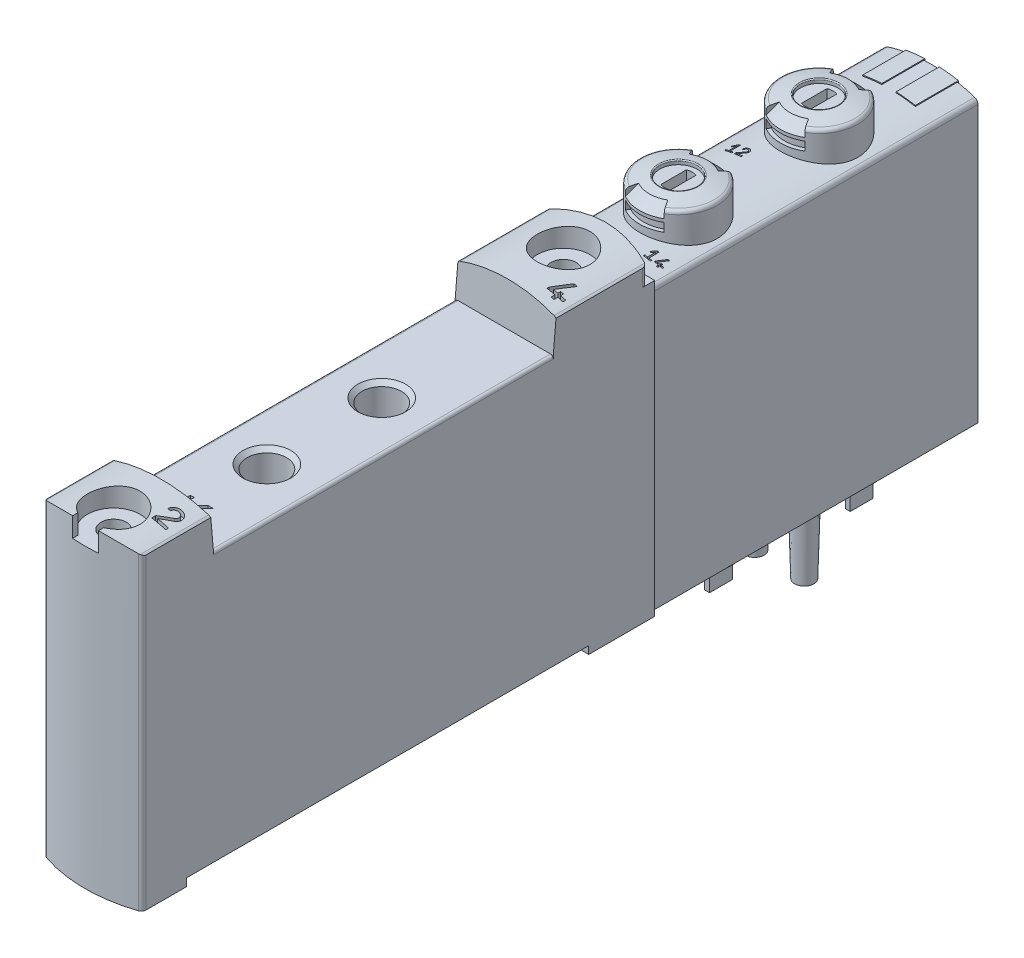
SolidWorks part; units mm, degrees
ref_plane "Front Plane" through (0, 0, 0) normal (0, 0, 1) x (1, 0, 0)
ref_plane "Top Plane" through (0, 0, 0) normal (0, 1, 0) x (1, 0, 0)
ref_plane "Right Plane" through (0, 0, 0) normal (1, 0, 0) x (0, 0, -1)
ref_plane "Plane1" through (0, 0, -23.2) normal (0, 0, 1) x (1, 0, 0)
sketch "Sketch1" plane through (0, 0, -23.2) normal (0, 0, 1) x (1, 0, 0)
  line L0 (-4.9, 29.2163) -> (-4.9, 0)
  line L1 (-4.9, 0) -> (4.9, 0)
  line L2 (4.9, 0) -> (4.9, 29.2163)
  arc A0 (4.9, 29.2163) -> (4.5517, 29.6927) centre (4.4, 29.2163) ccw
  arc A1 (4.5517, 29.6927) -> (-4.5517, 29.6927) centre (0, 15.4) ccw
  arc A2 (-4.5517, 29.6927) -> (-4.9, 29.2163) centre (-4.4, 29.2163) ccw
extrude "Boss-Extrude1" add sketch "Sketch1" along normal blind 34
ref_plane "Plane2" through (0, 0, 0) normal (1, 0, 0) x (0, 0, -1)
sketch "Sketch2" plane through (0, 0, 0) normal (1, 0, 0) x (0, 0, -1)
  line L0 (-10.88, 0.4) -> (-10.88, 0)
  line L1 (-10.88, 0) -> (23.22, 0)
  line L2 (23.22, 0) -> (23.22, 0.4)
  line L3 (23.22, 0.4) -> (-10.88, 0.4)
extrude "Cut-Extrude1" cut sketch "Sketch2" against normal blind 6 and the other way blind 6
ref_plane "Plane3" through (0, 0, 0) normal (0, 1, 0) x (1, 0, 0)
sketch "Sketch3" plane through (0, 0, 0) normal (0, 1, 0) x (1, 0, 0)
  line L0 (-3.15, 2.4653) -> (-3.15, -2.4653)
  line L1 (3.15, -2.4653) -> (3.15, 2.4653)
  arc A0 (-3.15, -2.4653) -> (3.15, -2.4653) centre (0, 0) ccw
  arc A1 (3.15, 2.4653) -> (-3.15, 2.4653) centre (0, 0) ccw
extrude "Cut-Extrude2" cut sketch "Sketch3" along normal blind 1.9
ref_plane "Plane4" through (0, 0, 0) normal (0, 1, 0) x (1, 0, 0)
sketch "Sketch4" plane through (0, 0, 0) normal (0, 1, 0) x (1, 0, 0)
  line L0 (-3.15, 17.1653) -> (-3.15, 12.2347)
  line L1 (3.15, 12.2347) -> (3.15, 17.1653)
  arc A0 (-3.15, 12.2347) -> (3.15, 12.2347) centre (0, 14.7) ccw
  arc A1 (3.15, 17.1653) -> (-3.15, 17.1653) centre (0, 14.7) ccw
extrude "Cut-Extrude3" cut sketch "Sketch4" along normal blind 1.9
ref_plane "Plane5" through (0, 0, 0) normal (1, 0, 0) x (0, 0, -1)
sketch "Sketch5" plane through (0, 0, 0) normal (1, 0, 0) x (0, 0, -1)
  line L0 (0, 2.1) -> (3.05, 2.1)
  line L1 (3.05, 2.1) -> (3.05, 1.1)
  line L2 (3.05, 1.1) -> (2.25, 1.1)
  line L3 (2.25, 1.1) -> (2.25, -1.4)
  line L4 (2.25, -1.4) -> (2.65, -1.4)
  line L5 (2.65, -1.4) -> (2.65, -1.72)
  line L6 (2.65, -1.72) -> (2.4306, -2.1)
  line L7 (2.4306, -2.1) -> (0, -2.1)
  line L8 (0, -2.1) -> (0, 2.1)
  line L9 (0, -2.1) -> (0, 2.1) construction
revolve "Revolve1" add sketch "Sketch5" angle 360 about L9
ref_plane "Plane6" through (0, 0, 0) normal (1, 0, 0) x (0, 0, -1)
sketch "Sketch6" plane through (0, 0, 0) normal (1, 0, 0) x (0, 0, -1)
  line L0 (14.7, 2.1) -> (17.75, 2.1)
  line L1 (17.75, 2.1) -> (17.75, 1.1)
  line L2 (17.75, 1.1) -> (16.95, 1.1)
  line L3 (16.95, 1.1) -> (16.95, -1.4)
  line L4 (16.95, -1.4) -> (17.35, -1.4)
  line L5 (17.35, -1.4) -> (17.35, -1.72)
  line L6 (17.35, -1.72) -> (17.1306, -2.1)
  line L7 (17.1306, -2.1) -> (14.7, -2.1)
  line L8 (14.7, -2.1) -> (14.7, 2.1)
  line L9 (14.7, -2.1) -> (14.7, 2.1) construction
revolve "Revolve2" add sketch "Sketch6" angle 360 about L9
ref_plane "Plane7" through (0, 0, -7.35) normal (0, 0, 1) x (1, 0, 0)
sketch "Sketch7" plane through (0, 0, -7.35) normal (0, 0, 1) x (1, 0, 0)
  line L0 (2.6, 0.4) -> (3.8, 0.4)
  line L1 (3.8, 0.4) -> (3.6, -6.9)
  line L2 (2.6, -7.0623) -> (2.6, 0.4)
  line L3 (2.6, -7.0623) -> (2.6, 0.4) construction
  arc A0 (3.6, -6.9) -> (2.6, -7.0623) centre (2.6, -3.9) cw
revolve "Revolve3" add sketch "Sketch7" angle 360 about L3
ref_plane "Plane8" through (0, 0, -7.35) normal (0, 0, 1) x (1, 0, 0)
sketch "Sketch8" plane through (0, 0, -7.35) normal (0, 0, 1) x (1, 0, 0)
  line L0 (-2.6, 0.4) -> (-1.4, 0.4)
  line L1 (-1.4, 0.4) -> (-1.6, -6.9)
  line L2 (-2.6, -7.0623) -> (-2.6, 0.4)
  line L3 (-2.6, -7.0623) -> (-2.6, 0.4) construction
  arc A0 (-1.6, -6.9) -> (-2.6, -7.0623) centre (-2.6, -3.9) cw
revolve "Revolve4" add sketch "Sketch8" angle 360 about L3
ref_plane "Plane9" through (0, -2.1, 0) normal (0, -1, 0) x (-1, 0, 0)
sketch "Sketch9" plane through (0, -2.1, 0) normal (0, -1, 0) x (-1, 0, 0)
  line L0 (-1.25, -1.2) -> (-0.75, -1.2)
  line L1 (-0.75, -1.2) -> (-0.75, 1.2)
  line L2 (-0.75, 1.2) -> (-1.25, 1.2)
  line L3 (-1.25, 1.2) -> (-1.25, -1.2)
extrude "Boss-Extrude2" add sketch "Sketch9" along normal blind 2.5
ref_plane "Plane10" through (0, -2.1, 0) normal (0, -1, 0) x (-1, 0, 0)
sketch "Sketch10" plane through (0, -2.1, 0) normal (0, -1, 0) x (-1, 0, 0)
  line L0 (0.75, -1.2) -> (1.25, -1.2)
  line L1 (1.25, -1.2) -> (1.25, 1.2)
  line L2 (1.25, 1.2) -> (0.75, 1.2)
  line L3 (0.75, 1.2) -> (0.75, -1.2)
extrude "Boss-Extrude3" add sketch "Sketch10" along normal blind 2.5
ref_plane "Plane11" through (0, -2.1, 0) normal (0, -1, 0) x (-1, 0, 0)
sketch "Sketch11" plane through (0, -2.1, 0) normal (0, -1, 0) x (-1, 0, 0)
  line L0 (-1.25, 13.5) -> (-0.75, 13.5)
  line L1 (-0.75, 13.5) -> (-0.75, 15.9)
  line L2 (-0.75, 15.9) -> (-1.25, 15.9)
  line L3 (-1.25, 15.9) -> (-1.25, 13.5)
extrude "Boss-Extrude4" add sketch "Sketch11" along normal blind 2.5
ref_plane "Plane12" through (0, -2.1, 0) normal (0, -1, 0) x (-1, 0, 0)
sketch "Sketch12" plane through (0, -2.1, 0) normal (0, -1, 0) x (-1, 0, 0)
  line L0 (0.75, 13.5) -> (1.25, 13.5)
  line L1 (1.25, 13.5) -> (1.25, 15.9)
  line L2 (1.25, 15.9) -> (0.75, 15.9)
  line L3 (0.75, 15.9) -> (0.75, 13.5)
extrude "Boss-Extrude5" add sketch "Sketch12" along normal blind 2.5
ref_plane "Plane13" through (0, 0, 0) normal (1, 0, 0) x (0, 0, -1)
sketch "Sketch13" plane through (0, 0, 0) normal (1, 0, 0) x (0, 0, -1)
  line L0 (-3.2, 33.13) -> (-1.25, 33.13)
  line L1 (-1.25, 33.13) -> (-1.25, 33.4583)
  line L2 (0.85, 32.8364) -> (0.85, 28.4)
  line L3 (0.85, 28.4) -> (-3.2, 28.4)
  line L4 (-3.2, 28.4) -> (-3.2, 33.13)
  line L5 (-3.2, 28.4) -> (-3.2, 33.7) construction
  arc A0 (-1.25, 33.4583) -> (-1.1362, 33.5574) centre (-1.15, 33.4583) cw
  arc A1 (-1.1362, 33.5574) -> (0.55, 33.2237) centre (-3.2, 18.7) cw
  arc A2 (0.55, 33.2237) -> (0.85, 32.8364) centre (0.45, 32.8364) cw
revolve "Revolve5" add sketch "Sketch13" angle 360 about L5
ref_plane "Plane14" through (0, 0, 0) normal (1, 0, 0) x (0, 0, -1)
sketch "Sketch14" plane through (0, 0, 0) normal (1, 0, 0) x (0, 0, -1)
  line L0 (11.5, 33.13) -> (13.45, 33.13)
  line L1 (13.45, 33.13) -> (13.45, 33.4583)
  line L2 (15.55, 32.8364) -> (15.55, 28.4)
  line L3 (15.55, 28.4) -> (11.5, 28.4)
  line L4 (11.5, 28.4) -> (11.5, 33.13)
  line L5 (11.5, 28.4) -> (11.5, 33.7) construction
  arc A0 (13.45, 33.4583) -> (13.5638, 33.5574) centre (13.55, 33.4583) cw
  arc A1 (13.5638, 33.5574) -> (15.25, 33.2237) centre (11.5, 18.7) cw
  arc A2 (15.25, 33.2237) -> (15.55, 32.8364) centre (15.15, 32.8364) cw
revolve "Revolve6" add sketch "Sketch14" angle 360 about L5
ref_plane "Plane15" through (0, 0, 0) normal (1, 0, 0) x (0, 0, -1)
sketch "Sketch15" plane through (0, 0, 0) normal (1, 0, 0) x (0, 0, -1)
  line L0 (-0.47, 33.7) -> (0.9, 32.33)
  line L1 (0.9, 32.33) -> (0.9, 32.05)
  line L2 (0.9, 32.05) -> (0.45, 32.05)
  line L3 (0.45, 32.05) -> (0.45, 31.15)
  line L4 (0.45, 31.15) -> (0.9, 31.15)
  line L5 (0.9, 31.15) -> (0.9, 30.5)
  line L6 (0.9, 30.5) -> (1.3, 30.5)
  line L7 (1.3, 30.5) -> (1.3, 33.7)
  line L8 (1.3, 33.7) -> (-0.47, 33.7)
  line L9 (-3.2, 30.5) -> (-3.2, 33.7) construction
revolve "Cut-Revolve1" cut sketch "Sketch15" angle 30 about L9 other way angle 30
ref_plane "Plane16" through (0, 0, 0) normal (1, 0, 0) x (0, 0, -1)
sketch "Sketch16" plane through (0, 0, 0) normal (1, 0, 0) x (0, 0, -1)
  line L0 (-7.7, 30.5) -> (-7.3, 30.5)
  line L1 (-7.3, 30.5) -> (-7.3, 31.15)
  line L2 (-7.3, 31.15) -> (-6.85, 31.15)
  line L3 (-6.85, 31.15) -> (-6.85, 32.05)
  line L4 (-6.85, 32.05) -> (-7.3, 32.05)
  line L5 (-7.3, 32.05) -> (-7.3, 32.33)
  line L6 (-7.3, 32.33) -> (-5.93, 33.7)
  line L7 (-5.93, 33.7) -> (-7.7, 33.7)
  line L8 (-7.7, 33.7) -> (-7.7, 30.5)
  line L9 (-3.2, 33.7) -> (-3.2, 30.5) construction
revolve "Cut-Revolve2" cut sketch "Sketch16" angle 30 about L9 other way angle 30
ref_plane "Plane17" through (0, 33.13, 0) normal (0, 1, 0) x (1, 0, 0)
sketch "Sketch17" plane through (0, 33.13, 0) normal (0, 1, 0) x (1, 0, 0)
  line L0 (0.5, -4.5344) -> (0.5, -1.8656)
  line L1 (-0.5, -1.8656) -> (-0.5, -4.5344)
  arc A0 (-0.5, -4.5344) -> (0.5, -4.5344) centre (0, -3.2) ccw
  arc A1 (0.5, -1.8656) -> (-0.5, -1.8656) centre (0, -3.2) ccw
extrude "Cut-Extrude4" cut sketch "Sketch17" against normal blind 1.7
ref_plane "Plane18" through (0, 0, 0) normal (1, 0, 0) x (0, 0, -1)
sketch "Sketch18" plane through (0, 0, 0) normal (1, 0, 0) x (0, 0, -1)
  line L0 (14.23, 33.7) -> (15.6, 32.33)
  line L1 (15.6, 32.33) -> (15.6, 32.05)
  line L2 (15.6, 32.05) -> (15.15, 32.05)
  line L3 (15.15, 32.05) -> (15.15, 31.15)
  line L4 (15.15, 31.15) -> (15.6, 31.15)
  line L5 (15.6, 31.15) -> (15.6, 30.5)
  line L6 (15.6, 30.5) -> (16, 30.5)
  line L7 (16, 30.5) -> (16, 33.7)
  line L8 (16, 33.7) -> (14.23, 33.7)
  line L9 (11.5, 30.5) -> (11.5, 33.7) construction
revolve "Cut-Revolve3" cut sketch "Sketch18" angle 30 about L9 other way angle 30
ref_plane "Plane19" through (0, 0, 0) normal (1, 0, 0) x (0, 0, -1)
sketch "Sketch19" plane through (0, 0, 0) normal (1, 0, 0) x (0, 0, -1)
  line L0 (7, 30.5) -> (7.4, 30.5)
  line L1 (7.4, 30.5) -> (7.4, 31.15)
  line L2 (7.4, 31.15) -> (7.85, 31.15)
  line L3 (7.85, 31.15) -> (7.85, 32.05)
  line L4 (7.85, 32.05) -> (7.4, 32.05)
  line L5 (7.4, 32.05) -> (7.4, 32.33)
  line L6 (7.4, 32.33) -> (8.77, 33.7)
  line L7 (8.77, 33.7) -> (7, 33.7)
  line L8 (7, 33.7) -> (7, 30.5)
  line L9 (11.5, 33.7) -> (11.5, 30.5) construction
revolve "Cut-Revolve4" cut sketch "Sketch19" angle 30 about L9 other way angle 30
ref_plane "Plane20" through (0, 33.13, 0) normal (0, 1, 0) x (1, 0, 0)
sketch "Sketch20" plane through (0, 33.13, 0) normal (0, 1, 0) x (1, 0, 0)
  line L0 (0.5, 10.1656) -> (0.5, 12.8344)
  line L1 (-0.5, 12.8344) -> (-0.5, 10.1656)
  arc A0 (-0.5, 10.1656) -> (0.5, 10.1656) centre (0, 11.5) ccw
  arc A1 (0.5, 12.8344) -> (-0.5, 12.8344) centre (0, 11.5) ccw
extrude "Cut-Extrude5" cut sketch "Sketch20" against normal blind 1.7
ref_plane "Plane21" through (0, 0, -23.3) normal (0, 0, 1) x (1, 0, 0)
sketch "Sketch21" plane through (0, 0, -23.3) normal (0, 0, 1) x (1, 0, 0)
  line L0 (0.75, 30.4814) -> (0.75, 27)
  line L1 (0.75, 27) -> (2.75, 27)
  line L2 (2.75, 27) -> (2.75, 30.2475)
  arc A0 (2.75, 30.2475) -> (0.75, 30.4814) centre (0, 15.4) ccw
extrude "Boss-Extrude6" add sketch "Sketch21" along normal blind 4.5
ref_plane "Plane22" through (0, 0, -23.3) normal (0, 0, 1) x (1, 0, 0)
sketch "Sketch22" plane through (0, 0, -23.3) normal (0, 0, 1) x (1, 0, 0)
  line L0 (-2.75, 30.2475) -> (-2.75, 27)
  line L1 (-2.75, 27) -> (-0.75, 27)
  line L2 (-0.75, 27) -> (-0.75, 30.4814)
  arc A0 (-0.75, 30.4814) -> (-2.75, 30.2475) centre (0, 15.4) ccw
extrude "Boss-Extrude7" add sketch "Sketch22" along normal blind 4.5
ref_plane "Plane23" through (0, 0, 0) normal (0, 1, 0) x (1, 0, 0)
sketch "Sketch23" plane through (0, 0, 0) normal (0, 1, 0) x (1, 0, 0)
  line L0 (5.125, -63.9426) -> (5.125, -10.8)
  line L1 (5.125, -10.8) -> (-5.125, -10.8)
  line L2 (-5.125, -10.8) -> (-5.125, -63.9426)
  arc A0 (-5.125, -63.9426) -> (-4.7845, -64.4165) centre (-4.625, -63.9426) ccw
  arc A1 (-4.7845, -64.4165) -> (4.7845, -64.4165) centre (0, -50.2) ccw
  arc A2 (4.7845, -64.4165) -> (5.125, -63.9426) centre (4.625, -63.9426) ccw
extrude "Boss-Extrude8" add sketch "Sketch23" along normal blind 33.1
ref_plane "Plane24" through (0, 0, 0) normal (1, 0, 0) x (0, 0, -1)
sketch "Sketch24" plane through (0, 0, 0) normal (1, 0, 0) x (0, 0, -1)
  line L0 (-57.7749, 38.9) -> (-56.9, 28.9)
  line L1 (-56.9, 28.9) -> (-21.4, 28.9)
  line L2 (-21.4, 28.9) -> (-20.5251, 38.9)
  line L3 (-20.5251, 38.9) -> (-57.7749, 38.9)
extrude "Cut-Extrude6" cut sketch "Sketch24" against normal blind 10 and the other way blind 10
ref_plane "Plane25" through (0, 30.4, 0) normal (0, 1, 0) x (1, 0, 0)
sketch "Sketch25" plane through (0, 30.4, 0) normal (0, 1, 0) x (1, 0, 0)
  line L0 (-5.125, -8.8) -> (-5.125, -12.0574)
  line L1 (5.125, -12.0574) -> (5.125, -8.8)
  line L2 (5.125, -8.8) -> (-5.125, -8.8)
  arc A0 (-5.125, -12.0574) -> (-4.7845, -11.5835) centre (-4.625, -12.0574) cw
  arc A1 (-4.7845, -11.5835) -> (4.7845, -11.5835) centre (0, -25.8) cw
  arc A2 (4.7845, -11.5835) -> (5.125, -12.0574) centre (4.625, -12.0574) cw
extrude "Cut-Extrude7" cut sketch "Sketch25" along normal blind 10
ref_plane "Plane26" through (0, 0, 0) normal (1, 0, 0) x (0, 0, -1)
sketch "Sketch26" plane through (0, 0, 0) normal (1, 0, 0) x (0, 0, -1)
  line L0 (-59.7, -0.2) -> (-17.7, -0.2)
  line L1 (-17.7, -0.2) -> (-17.7, 0.8)
  line L2 (-17.7, 0.8) -> (-59.7, 0.8)
  line L3 (-59.7, 0.8) -> (-59.7, -0.2)
extrude "Cut-Extrude8" cut sketch "Sketch26" against normal blind 10 and the other way blind 10
ref_plane "Plane27" through (0, 0, 10.8) normal (0, 0, 1) x (1, 0, 0)
sketch "Sketch27" plane through (0, 0, 10.8) normal (0, 0, 1) x (1, 0, 0)
  line L0 (-5.25, 35.1) -> (-5.25, 31.7999)
  line L1 (5.25, 31.7999) -> (5.25, 35.1)
  line L2 (5.25, 35.1) -> (-5.25, 35.1)
  arc A0 (-5.25, 31.7999) -> (-4.9138, 32.2723) centre (-4.75, 31.7999) cw
  arc A1 (-4.9138, 32.2723) -> (4.9138, 32.2723) centre (0, 18.1) cw
  arc A2 (4.9138, 32.2723) -> (5.25, 31.7999) centre (4.75, 31.7999) cw
extrude "Cut-Extrude9" cut sketch "Sketch27" along normal blind 55
ref_plane "Plane28" through (0, 0, 21.4) normal (0, 0, 1) x (1, 0, 0)
sketch "Sketch28" plane through (0, 0, 21.4) normal (0, 0, 1) x (1, 0, 0)
  line L0 (-4.825, 28.9) -> (4.825, 28.9)
  line L1 (5.125, 28.6) -> (5.125, 33.6)
  line L2 (5.125, 33.6) -> (-5.125, 33.6)
  line L3 (-5.125, 33.6) -> (-5.125, 28.6)
  arc A0 (-5.125, 28.6) -> (-4.825, 28.9) centre (-4.825, 28.6) cw
  arc A1 (4.825, 28.9) -> (5.125, 28.6) centre (4.825, 28.6) cw
extrude "Cut-Extrude10" cut sketch "Sketch28" along normal blind 35.5
ref_plane "Plane29" through (0, 33.1, 0) normal (0, 1, 0) x (1, 0, 0)
sketch "Sketch29" plane through (0, 33.1, 0) normal (0, 1, 0) x (1, 0, 0)
  line L0 (-1.35, -64.5958) -> (-1.35, -66)
  line L1 (-1.35, -66) -> (1.35, -66)
  line L2 (1.35, -66) -> (1.35, -64.5958)
  arc A0 (1.35, -64.5958) -> (-1.35, -64.5958) centre (0, -62.2) ccw
extrude "Cut-Extrude11" cut sketch "Sketch29" against normal blind 2.1 and the other way blind 2.1
ref_plane "Plane30" through (0, 0, 0) normal (1, 0, 0) x (0, 0, -1)
sketch "Sketch30" plane through (0, 0, 0) normal (1, 0, 0) x (0, 0, -1)
  line L0 (-62.2, 31) -> (-60.875, 31)
  line L1 (-60.875, 31) -> (-60.875, 0)
  line L2 (-60.875, 0) -> (-62.2, 0)
  line L3 (-62.2, 0) -> (-62.2, 31)
  line L4 (-62.2, 0) -> (-62.2, 31) construction
revolve "Cut-Revolve5" cut sketch "Sketch30" angle 360 about L4
ref_plane "Plane31" through (0, 0, 0) normal (1, 0, 0) x (0, 0, -1)
sketch "Sketch31" plane through (0, 0, 0) normal (1, 0, 0) x (0, 0, -1)
  line L0 (-15.2, 33.2) -> (-12.45, 33.2)
  line L1 (-12.45, 33.2) -> (-12.45, 31)
  line L2 (-12.45, 31) -> (-13.875, 31)
  line L3 (-13.875, 31) -> (-13.875, 0)
  line L4 (-13.875, 0) -> (-15.2, 0)
  line L5 (-15.2, 0) -> (-15.2, 33.2)
  line L6 (-15.2, 0) -> (-15.2, 33.2) construction
revolve "Cut-Revolve6" cut sketch "Sketch31" angle 360 about L6
ref_plane "Plane32" through (0, 0, 0) normal (1, 0, 0) x (0, 0, -1)
sketch "Sketch32" plane through (0, 0, 0) normal (1, 0, 0) x (0, 0, -1)
  line L0 (-34.2, 28.9) -> (-31.7, 28.9)
  line L1 (-31.7, 28.9) -> (-32.133, 28.467)
  line L2 (-32.133, 28.467) -> (-32.133, 22.3)
  line L3 (-32.133, 22.3) -> (-34.2, 22.3)
  line L4 (-34.2, 22.3) -> (-34.2, 28.9)
  line L5 (-34.2, 22.3) -> (-34.2, 28.9) construction
revolve "Cut-Revolve7" cut sketch "Sketch32" angle 360 about L5
cosmetic thread "Cosmetic Thread1" parameters "D1"=4.5, "D2"=5
ref_plane "Plane33" through (0, 0, 0) normal (1, 0, 0) x (0, 0, -1)
sketch "Sketch33" plane through (0, 0, 0) normal (1, 0, 0) x (0, 0, -1)
  line L0 (-46.2, 28.9) -> (-43.7, 28.9)
  line L1 (-43.7, 28.9) -> (-44.133, 28.467)
  line L2 (-44.133, 28.467) -> (-44.133, 22.3)
  line L3 (-44.133, 22.3) -> (-46.2, 22.3)
  line L4 (-46.2, 22.3) -> (-46.2, 28.9)
  line L5 (-46.2, 22.3) -> (-46.2, 28.9) construction
revolve "Cut-Revolve8" cut sketch "Sketch33" angle 360 about L5
cosmetic thread "Cosmetic Thread2" parameters "D1"=4.5, "D2"=5
ref_plane "Plane34" through (0, 0, 0) normal (1, 0, 0) x (0, 0, -1)
sketch "Sketch34" plane through (0, 0, 0) normal (1, 0, 0) x (0, 0, -1)
  line L0 (-29.2, 7.3) -> (-27.1, 7.3)
  line L1 (-27.1, 7.3) -> (-27.1, 2.8)
  line L2 (-27.1, 2.8) -> (-26.2, 2.8)
  line L3 (-26.2, 2.8) -> (-26.2, 1.3)
  line L4 (-26.2, 1.3) -> (-25.7, 0.8)
  line L5 (-25.7, 0.8) -> (-29.2, 0.8)
  line L6 (-29.2, 0.8) -> (-29.2, 7.3)
  line L7 (-29.2, 0.8) -> (-29.2, 7.3) construction
revolve "Cut-Revolve9" cut sketch "Sketch34" angle 360 about L7
ref_plane "Plane35" through (0, 0, 0) normal (1, 0, 0) x (0, 0, -1)
sketch "Sketch35" plane through (0, 0, 0) normal (1, 0, 0) x (0, 0, -1)
  line L0 (-40.2, 7.3) -> (-38.1, 7.3)
  line L1 (-38.1, 7.3) -> (-38.1, 2.8)
  line L2 (-38.1, 2.8) -> (-37.2, 2.8)
  line L3 (-37.2, 2.8) -> (-37.2, 1.3)
  line L4 (-37.2, 1.3) -> (-36.7, 0.8)
  line L5 (-36.7, 0.8) -> (-40.2, 0.8)
  line L6 (-40.2, 0.8) -> (-40.2, 7.3)
  line L7 (-40.2, 0.8) -> (-40.2, 7.3) construction
revolve "Cut-Revolve10" cut sketch "Sketch35" angle 360 about L7
ref_plane "Plane36" through (0, 0, 0) normal (1, 0, 0) x (0, 0, -1)
sketch "Sketch36" plane through (0, 0, 0) normal (1, 0, 0) x (0, 0, -1)
  line L0 (-51.2, 7.3) -> (-49.1, 7.3)
  line L1 (-49.1, 7.3) -> (-49.1, 2.8)
  line L2 (-49.1, 2.8) -> (-48.2, 2.8)
  line L3 (-48.2, 2.8) -> (-48.2, 1.3)
  line L4 (-48.2, 1.3) -> (-47.7, 0.8)
  line L5 (-47.7, 0.8) -> (-51.2, 0.8)
  line L6 (-51.2, 0.8) -> (-51.2, 7.3)
  line L7 (-51.2, 0.8) -> (-51.2, 7.3) construction
revolve "Cut-Revolve11" cut sketch "Sketch36" angle 360 about L7
ref_plane "Plane37" through (0, 33.1, 0) normal (0, 1, 0) x (1, 0, 0)
sketch "Sketch37" plane through (0, 33.1, 0) normal (0, 1, 0) x (1, 0, 0)
  line L0 (-3.3985, 5.738) -> (-3.2978, 5.6676)
  line L1 (-3.2978, 5.6676) -> (-3.075, 5.9858)
  line L2 (-3.075, 5.9858) -> (-3.075, 5.15)
  line L3 (-3.075, 5.15) -> (-3.375, 5.15)
  line L4 (-3.375, 5.15) -> (-3.375, 5)
  line L5 (-3.375, 5) -> (-2.625, 5)
  line L6 (-2.625, 5) -> (-2.625, 5.15)
  line L7 (-2.625, 5.15) -> (-2.925, 5.15)
  line L8 (-2.925, 5.15) -> (-2.925, 6.2)
  line L9 (-2.925, 6.2) -> (-3.075, 6.2)
  line L10 (-3.075, 6.2) -> (-3.3985, 5.738)
extrude "Cut-Extrude12" cut sketch "Sketch37" against normal blind 3.5 and the other way blind 3.5
ref_plane "Plane38" through (0, 33.1, 0) normal (0, 1, 0) x (1, 0, 0)
sketch "Sketch38" plane through (0, 33.1, 0) normal (0, 1, 0) x (1, 0, 0)
  line L0 (-2.3625, 5.8375) -> (-2.2125, 5.8375)
  line L1 (-1.8546, 5.6826) -> (-2.3625, 5.2057)
  line L2 (-2.3625, 5.2057) -> (-2.3625, 5)
  line L3 (-2.3625, 5) -> (-1.6375, 5)
  line L4 (-1.6375, 5) -> (-1.6375, 5.15)
  line L5 (-1.6375, 5.15) -> (-2.2027, 5.15)
  line L6 (-2.2027, 5.15) -> (-1.7519, 5.5732)
  arc A0 (-2.2125, 5.8375) -> (-1.8546, 5.6826) centre (-2, 5.8375) cw
  arc A1 (-1.7519, 5.5732) -> (-2.3625, 5.8375) centre (-2, 5.8375) ccw
extrude "Cut-Extrude13" cut sketch "Sketch38" against normal blind 3.5 and the other way blind 3.5
ref_plane "Plane39" through (0, 33.1, 0) normal (0, 1, 0) x (1, 0, 0)
sketch "Sketch39" plane through (0, 33.1, 0) normal (0, 1, 0) x (1, 0, 0)
  line L0 (2.1015, -8.262) -> (2.2022, -8.3324)
  line L1 (2.2022, -8.3324) -> (2.425, -8.0142)
  line L2 (2.425, -8.0142) -> (2.425, -8.85)
  line L3 (2.425, -8.85) -> (2.125, -8.85)
  line L4 (2.125, -8.85) -> (2.125, -9)
  line L5 (2.125, -9) -> (2.875, -9)
  line L6 (2.875, -9) -> (2.875, -8.85)
  line L7 (2.875, -8.85) -> (2.575, -8.85)
  line L8 (2.575, -8.85) -> (2.575, -7.8)
  line L9 (2.575, -7.8) -> (2.425, -7.8)
  line L10 (2.425, -7.8) -> (2.1015, -8.262)
extrude "Cut-Extrude14" cut sketch "Sketch39" against normal blind 3.5 and the other way blind 3.5
ref_plane "Plane40" through (0, 33.1, 0) normal (0, 1, 0) x (1, 0, 0)
sketch "Sketch40" plane through (0, 33.1, 0) normal (0, 1, 0) x (1, 0, 0)
  line L0 (3.085, -8.8) -> (3.5, -8.8)
  line L1 (3.5, -8.8) -> (3.5, -9)
  line L2 (3.5, -9) -> (3.65, -9)
  line L3 (3.65, -9) -> (3.65, -8.8)
  line L4 (3.65, -8.8) -> (3.915, -8.8)
  line L5 (3.915, -8.8) -> (3.915, -8.65)
  line L6 (3.915, -8.65) -> (3.65, -8.65)
  line L7 (3.65, -8.65) -> (3.65, -8.5)
  line L8 (3.65, -8.5) -> (3.5, -8.5)
  line L9 (3.5, -8.5) -> (3.5, -8.65)
  line L10 (3.5, -8.65) -> (3.2699, -8.65)
  line L11 (3.2699, -8.65) -> (3.6663, -7.8)
  line L12 (3.6663, -7.8) -> (3.5008, -7.8)
  line L13 (3.5008, -7.8) -> (3.085, -8.6917)
  line L14 (3.085, -8.6917) -> (3.085, -8.8)
extrude "Cut-Extrude15" cut sketch "Sketch40" against normal blind 3.5 and the other way blind 3.5
ref_plane "Plane41" through (0, 33.1, 0) normal (0, 1, 0) x (1, 0, 0)
sketch "Sketch41" plane through (0, 33.1, 0) normal (0, 1, 0) x (1, 0, 0)
  line L0 (2.67, -19.6) -> (3.5, -19.6)
  line L1 (3.5, -19.6) -> (3.5, -20)
  line L2 (3.5, -20) -> (3.8, -20)
  line L3 (3.8, -20) -> (3.8, -19.6)
  line L4 (3.8, -19.6) -> (4.33, -19.6)
  line L5 (4.33, -19.6) -> (4.33, -19.3)
  line L6 (4.33, -19.3) -> (3.8, -19.3)
  line L7 (3.8, -19.3) -> (3.8, -19)
  line L8 (3.8, -19) -> (3.5, -19)
  line L9 (3.5, -19) -> (3.5, -19.3)
  line L10 (3.5, -19.3) -> (3.0399, -19.3)
  line L11 (3.0399, -19.3) -> (3.8326, -17.6)
  line L12 (3.8326, -17.6) -> (3.5016, -17.6)
  line L13 (3.5016, -17.6) -> (2.67, -19.3834)
  line L14 (2.67, -19.3834) -> (2.67, -19.6)
extrude "Cut-Extrude16" cut sketch "Sketch41" against normal blind 1 and the other way blind 1
ref_plane "Plane42" through (0, 33.1, 0) normal (0, 1, 0) x (1, 0, 0)
sketch "Sketch42" plane through (0, 33.1, 0) normal (0, 1, 0) x (1, 0, 0)
  line L0 (2.775, -59.325) -> (3.075, -59.325)
  line L1 (3.7909, -59.6349) -> (2.775, -60.5885)
  line L2 (2.775, -60.5885) -> (2.775, -61)
  line L3 (2.775, -61) -> (4.225, -61)
  line L4 (4.225, -61) -> (4.225, -60.7)
  line L5 (4.225, -60.7) -> (3.0946, -60.7)
  line L6 (3.0946, -60.7) -> (3.9962, -59.8536)
  arc A0 (3.075, -59.325) -> (3.7909, -59.6349) centre (3.5, -59.325) cw
  arc A1 (3.9962, -59.8536) -> (2.775, -59.325) centre (3.5, -59.325) ccw
extrude "Cut-Extrude17" cut sketch "Sketch42" against normal blind 1 and the other way blind 1
ref_plane "Plane43" through (0, 33.1, 0) normal (0, 1, 0) x (1, 0, 0)
sketch "Sketch43" plane through (0, 33.1, 0) normal (0, 1, 0) x (1, 0, 0)
  line L0 (-1.2, -53) -> (-1.2, -56)
  line L1 (-1.2, -56) -> (-0.78, -56)
  line L2 (-0.78, -56) -> (-0.78, -54.95)
  line L3 (-0.78, -54.95) -> (-0.3273, -54.5041)
  line L4 (-0.3273, -54.5041) -> (0.66, -56)
  line L5 (0.66, -56) -> (1.2, -56)
  line L6 (1.2, -56) -> (0, -54.1818)
  line L7 (0, -54.1818) -> (1.2, -53)
  line L8 (1.2, -53) -> (0.66, -53)
  line L9 (0.66, -53) -> (-0.78, -54.4182)
  line L10 (-0.78, -54.4182) -> (-0.78, -53)
  line L11 (-0.78, -53) -> (-1.2, -53)
extrude "Cut-Extrude18" cut sketch "Sketch43" against normal blind 4.5 and the other way blind 4.5
